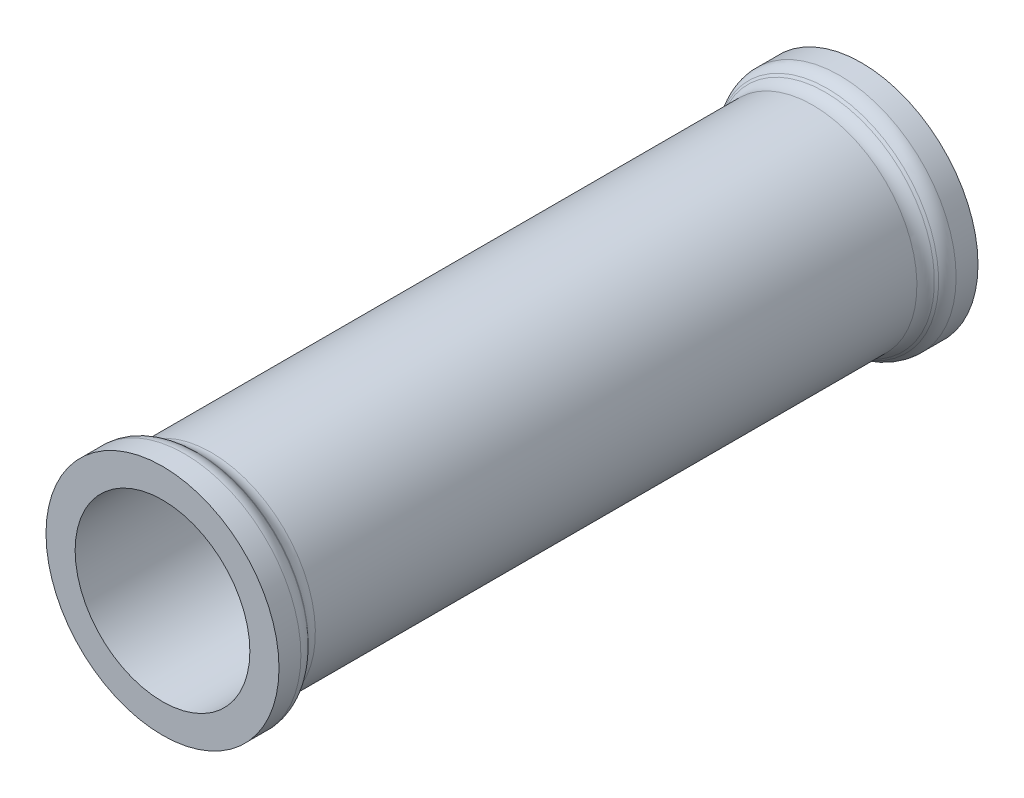
SolidWorks part; units mm, degrees
ref_plane "Front Plane" through (0, 0, 0) normal (0, 0, 1) x (1, 0, 0)
ref_plane "Top Plane" through (0, 0, 0) normal (0, 1, 0) x (1, 0, 0)
ref_plane "Right Plane" through (0, 0, 0) normal (1, 0, 0) x (0, 0, -1)
sketch "Sketch1" plane through (0, 0, 0) normal (1, 0, 0) x (0, 0, -1)
  line L0 (0, 0) -> (-120, 0)
  line L1 (-120, 0) -> (-120, -20)
  line L3 (0, -20) -> (0, 0)
  line L4 (-120, -20) -> (-116.2426, -20)
  line L5 (-114.1213, -19.1213) -> (-113.7574, -18.7574)
  line L6 (-111.636, -17.8787) -> (-8.364, -17.8787)
  line L7 (-6.2426, -18.7574) -> (-5.8787, -19.1213)
  line L8 (-3.7574, -20) -> (0, -20)
  arc A0 (-5.8787, -19.1213) -> (-3.7574, -20) centre (-3.7574, -17) ccw
  arc A1 (-8.364, -17.8787) -> (-6.2426, -18.7574) centre (-8.364, -20.8787) cw
  arc A2 (-113.7574, -18.7574) -> (-111.636, -17.8787) centre (-111.636, -20.8787) cw
  arc A3 (-116.2426, -20) -> (-114.1213, -19.1213) centre (-116.2426, -17) ccw
  point P11 (-5, -20)
  point P14 (-7.1213, -17.8787)
  point P17 (-112.8787, -17.8787)
  point P20 (-115, -20)
  dimension "D8" = 3
  dimension "D1" = 120
  dimension "D2" = 20
  dimension "D3" = 5
  dimension "D4" = 5
  dimension "D5" = 3
  dimension "D6" = 3
  dimension "D7" = 103.2721
revolve "Revolve2" add sketch "Sketch1" angle 360 about L0
sketch "Sketch2" plane through (0, 0, 0) normal (0, 0, -1) x (-1, 0, 0)
  circle A0 centre (0, 0) radius 15
  dimension "D1" = 30
extrude "Cut-Extrude1" cut sketch "Sketch2" against normal through all
